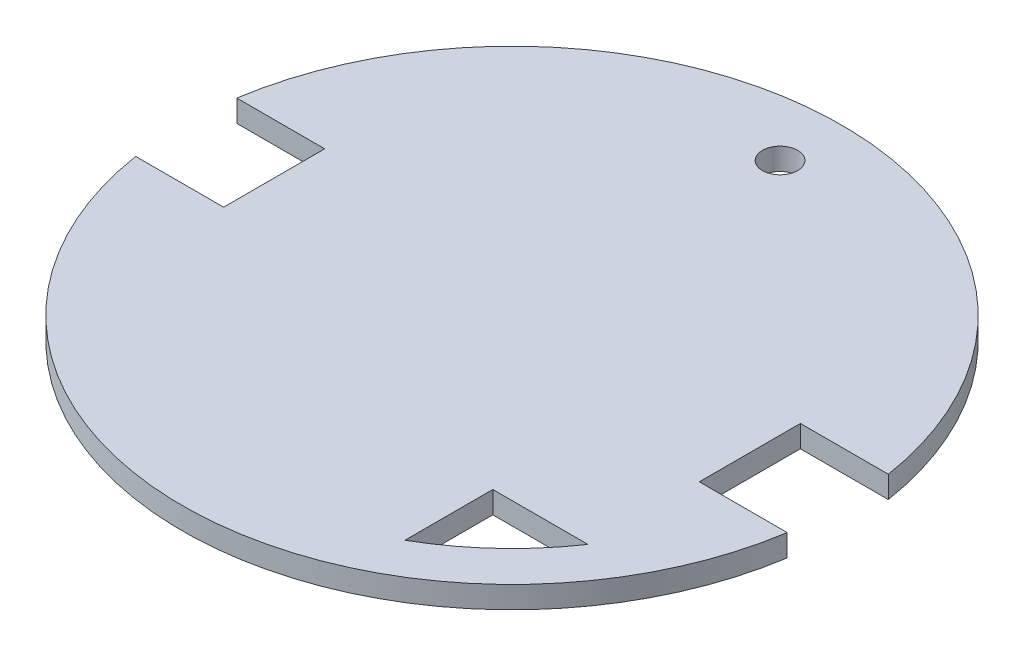
SolidWorks part; units mm, degrees
ref_plane "Front Plane" through (0, 0, 0) normal (0, 0, 1) x (1, 0, 0)
ref_plane "Top Plane" through (0, 0, 0) normal (0, 1, 0) x (1, 0, 0)
ref_plane "Right Plane" through (0, 0, 0) normal (1, 0, 0) x (0, 0, -1)
sketch "Sketch1" plane through (0, 0, 0) normal (0, 1, 0) x (1, 0, 0)
  circle A0 centre (-5.9358, 0) radius 75
  dimension "D1" = 150
extrude "Boss-Extrude1" add sketch "Sketch1" along normal blind 5
sketch "Sketch2" plane through (0, 5, 0) normal (0, 1, 0) x (1, 0, 0)
  line L0 (-80.0489, 11.5) -> (-80.0489, -11.5)
  line L1 (-80.0489, 11.5) -> (-60.0489, 11.5)
  line L2 (-80.0489, -11.5) -> (-60.0489, -11.5)
  line L3 (-60.0489, 11.5) -> (-60.0489, -11.5)
  line L4 (68.1773, 11.5) -> (68.1773, -11.5)
  line L5 (68.1773, 11.5) -> (48.1773, 11.5)
  line L6 (68.1773, -11.5) -> (48.1773, -11.5)
  line L7 (48.1773, 11.5) -> (48.1773, -11.5)
  line L8 (-80.0489, 11.5) -> (-80.0489, -11.5)
  line L9 (-80.0489, 11.5) -> (-89.004, 11.5)
  line L10 (-80.0489, -11.5) -> (-89.004, -11.5)
  line L11 (-89.004, 11.5) -> (-89.004, -11.5)
  line L12 (68.1773, 11.5) -> (68.1773, -11.5)
  line L13 (68.1773, 11.5) -> (83.1163, 11.5)
  line L14 (68.1773, -11.5) -> (83.1163, -11.5)
  line L15 (83.1163, 11.5) -> (83.1163, -11.5)
  line L16 (47.8485, -36.5) -> (26.2006, -36.5)
  line L17 (26.2006, -36.5) -> (26.2006, -56.5)
  circle A0 centre (-5.9358, 0) radius 75 construction
  circle A1 centre (-5.9358, 0) radius 65
  circle A2 centre (-5.9489, 61) radius 4
  circle M9 centre (-5.9358, 0) radius 75
  dimension "D3" = 130
  dimension "D4" = 25
  dimension "D7" = 8
  dimension "D1" = 20
  dimension "D2" = 23
  dimension "D5" = 20
  dimension "D6" = 21.6479
  dimension "D8" = 54.1
  dimension "D9" = 54.1262
extrude "Cut-Extrude1" cut sketch "Sketch2" against normal blind 5 contours L9 L11 L10 M9 | A1 L1 L0 L2 | L1 A1 L2 L3 | L6 A1 L5 L7 | A1 L6 L4 L5 | L15 L13 L14 M9 | L17 A1 L16 | A2 | L0 M9 | L4 M9
